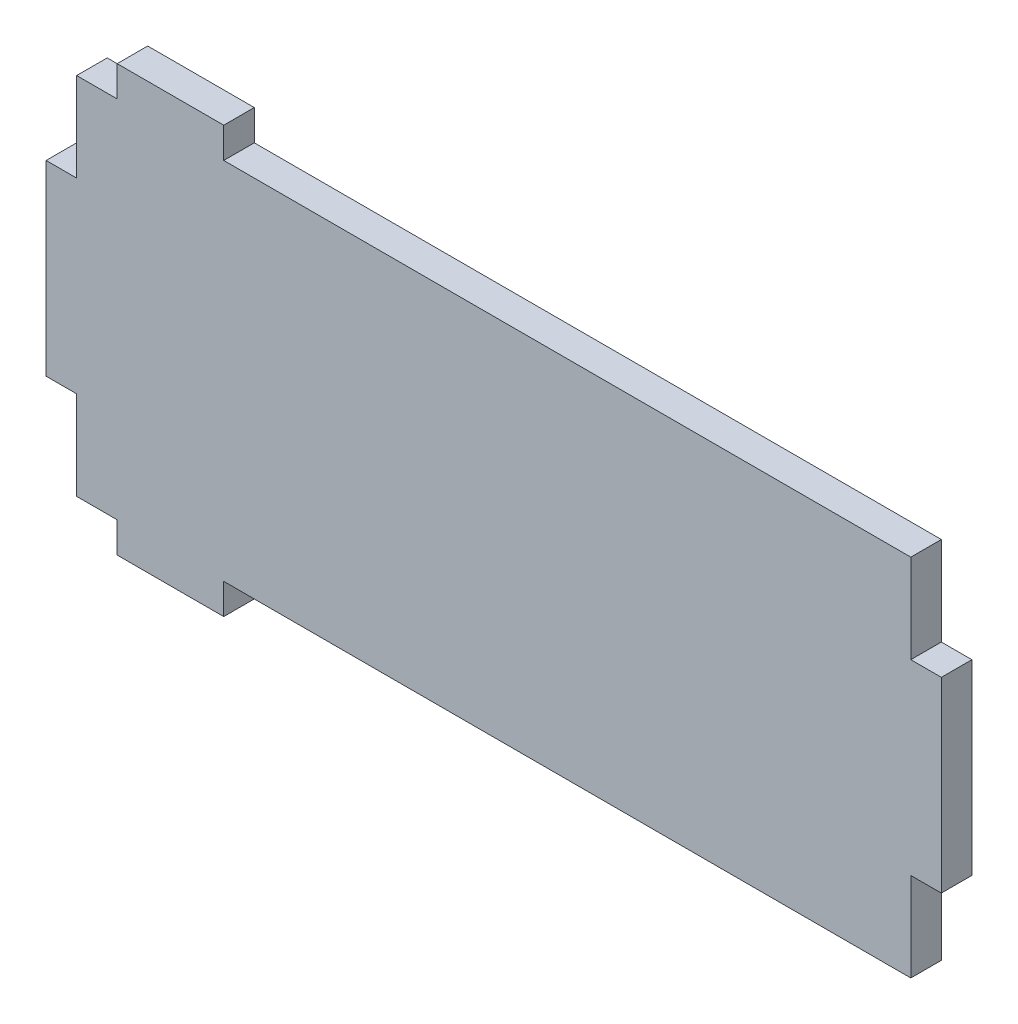
SolidWorks part; units mm, degrees
ref_plane "Front Plane" through (0, 0, 0) normal (0, 0, 1) x (1, 0, 0)
ref_plane "Top Plane" through (0, 0, 0) normal (0, 1, 0) x (1, 0, 0)
ref_plane "Right Plane" through (0, 0, 0) normal (1, 0, 0) x (0, 0, -1)
sketch "Sketch1" plane through (0, 0, 0) normal (0, 0, 1) x (1, 0, 0)
  line L1 (-80.01, 32.5755) -> (80.01, 32.5755)
  line L2 (-80.01, 32.5755) -> (-80.01, -32.5755)
  line L3 (-80.01, -32.5755) -> (80.01, -32.5755)
  line L4 (80.01, 32.5755) -> (80.01, -32.5755)
  line L5 (-80.01, 32.5755) -> (80.01, -32.5755) construction
  line L6 (-80.01, -32.5755) -> (80.01, 32.5755) construction
  point P0 (0, 0)
  dimension "D1" = 65.151
  dimension "D2" = 160.02
extrude "Boss-Extrude1" add sketch "Sketch1" along normal blind 5.461
sketch "Sketch2" plane through (0, 0, 5.461) normal (0, 0, 1) x (1, 0, 0)
  line L1 (-80.01, 32.5755) -> (-74.549, 32.5755)
  line L2 (-80.01, 32.5755) -> (-80.01, 16.7005)
  line L3 (-80.01, 16.7005) -> (-74.549, 16.7005)
  line L4 (-74.549, 32.5755) -> (-74.549, 16.7005)
  line L5 (-80.01, -32.5755) -> (-74.549, -32.5755)
  line L6 (-80.01, -32.5755) -> (-80.01, -16.7005)
  line L7 (-80.01, -16.7005) -> (-74.549, -16.7005)
  line L8 (-74.549, -32.5755) -> (-74.549, -16.7005)
  line L9 (80.01, 32.5755) -> (74.549, 32.5755)
  line L10 (80.01, 32.5755) -> (80.01, 16.7005)
  line L11 (80.01, 16.7005) -> (74.549, 16.7005)
  line L12 (74.549, 32.5755) -> (74.549, 16.7005)
  line L13 (80.01, -32.5755) -> (74.549, -32.5755)
  line L14 (80.01, -32.5755) -> (80.01, -16.7005)
  line L15 (80.01, -16.7005) -> (74.549, -16.7005)
  line L16 (74.549, -32.5755) -> (74.549, -16.7005)
  dimension "D1" = 15.875
  dimension "D2" = 5.461
extrude "Cut-Extrude1" cut sketch "Sketch2" against normal through all
sketch "Sketch4" plane through (0, 0, 5.461) normal (0, 0, 1) x (1, 0, 0)
  line L0 (74.549, 32.5755) -> (-74.549, 32.5755) construction
  line L1 (-67.31, 32.5755) -> (-48.26, 32.5755)
  line L2 (-67.31, 32.5755) -> (-67.31, 38.0365)
  line L3 (-67.31, 38.0365) -> (-48.26, 38.0365)
  line L4 (-48.26, 32.5755) -> (-48.26, 38.0365)
  line L5 (-74.549, -32.5755) -> (74.549, -32.5755) construction
  line L6 (-67.31, -32.5755) -> (-48.26, -32.5755)
  line L7 (-67.31, -32.5755) -> (-67.31, -38.0365)
  line L8 (-67.31, -38.0365) -> (-48.26, -38.0365)
  line L9 (-48.26, -32.5755) -> (-48.26, -38.0365)
  line L11 (-74.549, 16.7005) -> (-74.549, 32.5755) construction
  dimension "D1" = 19.05
  dimension "D2" = 7.239
  dimension "D3" = 5.461
extrude "Boss-Extrude3" add sketch "Sketch4" against normal up to surface (5.461 mm away) up to face at (0, 0, 0)
equation "\"D1@Sketch1\"=1.85+.215+.5"
